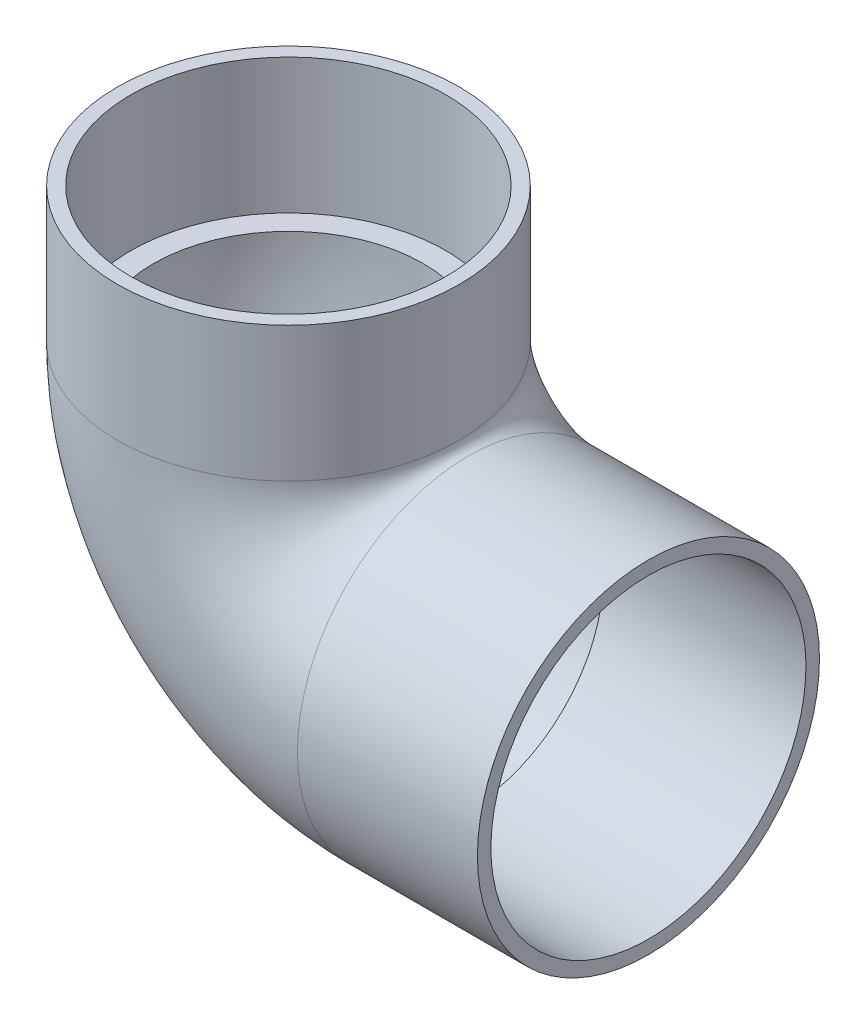
SolidWorks part; units mm, degrees
ref_plane "Front Plane" through (0, 0, 0) normal (0, 0, 1) x (1, 0, 0)
ref_plane "Top Plane" through (0, 0, 0) normal (0, 1, 0) x (1, 0, 0)
ref_plane "Right Plane" through (0, 0, 0) normal (1, 0, 0) x (0, 0, -1)
sketch "Sketch1" plane through (0, 0, 0) normal (0, 0, 1) x (1, 0, 0)
  line L0 (0, 88.9) -> (0, 50.8)
  line L1 (50.8, 0) -> (101.6, 0)
  arc A0 (50.8, 0) -> (0, 50.8) centre (50.8, 50.8) cw
  point P6 (0, 0)
  dimension "D3" = 50.8
  dimension "D1" = 101.6
  dimension "D2" = 88.9
ref_plane "Plane1" through (0, 88.9, 0) normal (0, 1, 0) x (1, 0, 0)
sketch "Sketch2" plane through (0, 88.9, 0) normal (0, 1, 0) x (1, 0, 0)
  circle A0 centre (0, 0) radius 48.26
  circle A1 centre (0, 0) radius 38.1
  dimension "D1" = 96.52
  dimension "D2" = 76.2
sweep "Sweep1" add profiles "Sketch2" path "Sketch1"
sketch "Sketch3" plane through (101.6, 0, 0) normal (1, 0, 0) x (0, 0, -1)
  circle A0 centre (0, 0) radius 44.45
  circle A1 centre (0, 0) radius 38.1
  circle A2 centre (0, 0) radius 38.1 construction
  dimension "D1" = 88.9
extrude "Cut-Extrude1" cut sketch "Sketch3" against normal blind 57.15
sketch "Sketch4" plane through (0, 88.9, 0) normal (0, 1, 0) x (1, 0, 0)
  circle A0 centre (0, 0) radius 38.1
  circle A1 centre (0, 0) radius 44.45
  circle A2 centre (0, 0) radius 38.1 construction
  dimension "D1" = 88.9
extrude "Cut-Extrude2" cut sketch "Sketch4" against normal blind 38.1
